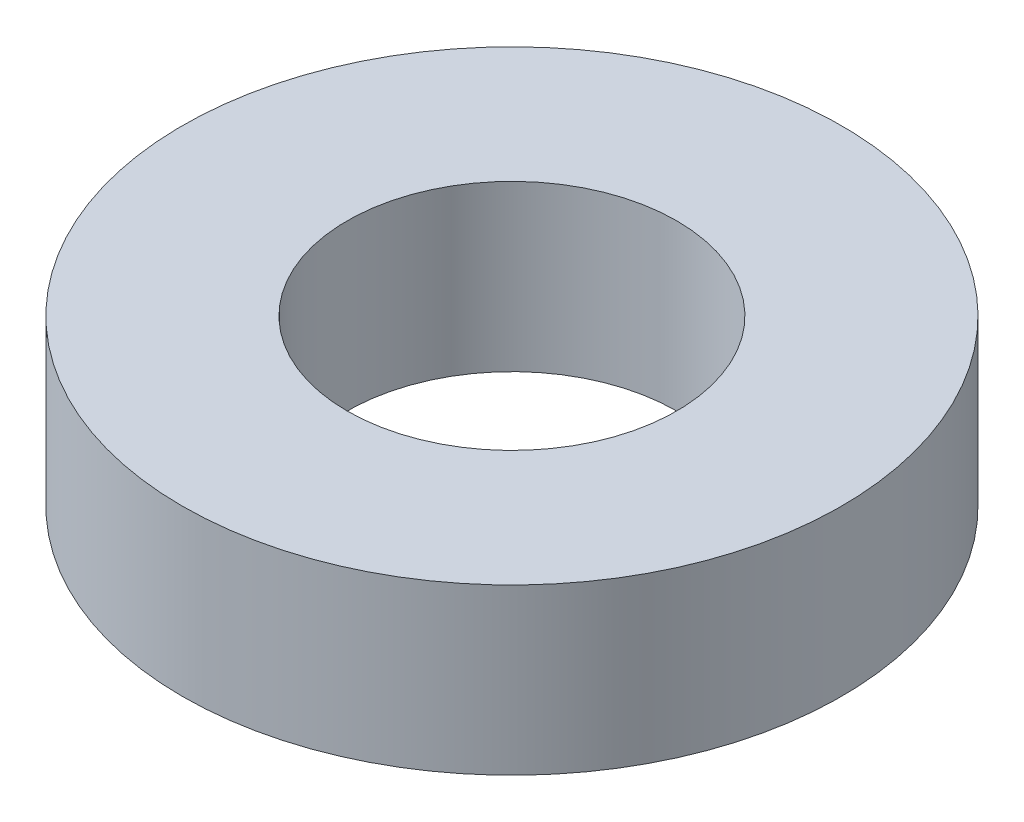
SolidWorks part; units mm, degrees
ref_plane "Front Plane" through (0, 0, 0) normal (0, 0, 1) x (1, 0, 0)
ref_plane "Top Plane" through (0, 0, 0) normal (0, 1, 0) x (1, 0, 0)
ref_plane "Right Plane" through (0, 0, 0) normal (1, 0, 0) x (0, 0, -1)
sketch "Sketch1" plane through (0, 0, 0) normal (0, 1, 0) x (1, 0, 0)
  circle A0 centre (0, 0) radius 3
  dimension "D1" = 6
extrude "Boss-Extrude1" add sketch "Sketch1" along normal blind 1.5
sketch "Sketch2" plane through (0, 1.5, 0) normal (0, 1, 0) x (1, 0, 0)
  circle A0 centre (0, 0) radius 1.5
  dimension "D1" = 3
extrude "Cut-Extrude1" cut sketch "Sketch2" against normal up to surface (1.5 mm away) up to face at (0, 0, 3)
